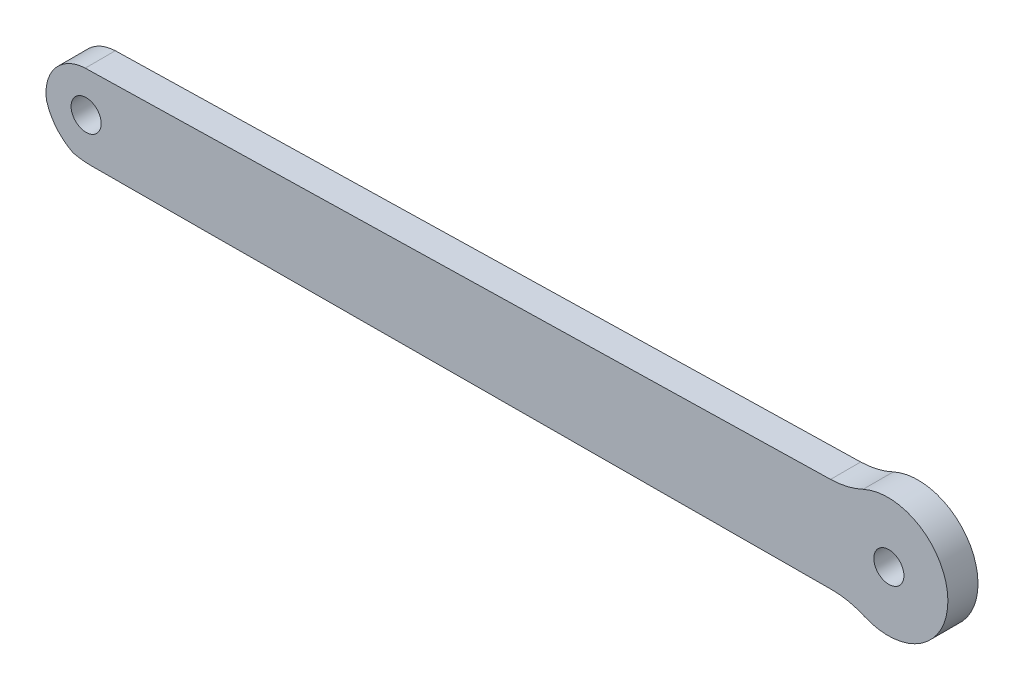
SolidWorks part; units mm, degrees
ref_plane "Front Plane" through (0, 0, 0) normal (0, 0, 1) x (1, 0, 0)
ref_plane "Top Plane" through (0, 0, 0) normal (0, 1, 0) x (1, 0, 0)
ref_plane "Right Plane" through (0, 0, 0) normal (1, 0, 0) x (0, 0, -1)
sketch "Model" plane through (0, 0, 0) normal (0, 0, 1) x (1, 0, 0)
  line L0 (49.9685, 21.05) -> (105.6188, 21.2894)
  line L1 (31.2271, 29.1011) -> (105.502, 30.7477)
  line L2 (49.9685, 21.05) -> (31.8741, 20.972)
  circle A0 centre (31.3157, 25.1021) radius 1.5
  circle A1 centre (111.3096, 26.0896) radius 1.5
  arc A2 (108.8793, 20.6038) -> (105.6188, 21.2894) centre (105.6393, 13.2911) ccw
  arc A3 (105.502, 30.7477) -> (108.7446, 31.5137) centre (105.3244, 38.7462) ccw
  arc A4 (31.2271, 29.1011) -> (27.3629, 24.4071) centre (31.3963, 25.0243) ccw
  arc A5 (27.3629, 24.4071) -> (30.0312, 21.1791) centre (32.3467, 25.81) ccw
  arc A6 (30.0312, 21.1791) -> (31.8741, 20.972) centre (31.8398, 28.9726) ccw
  arc A7 (108.8793, 20.6038) -> (108.7446, 31.5137) centre (111.2267, 26.0885) ccw
extrude "Boss-Extrude1" add sketch "Model" along normal blind 3
